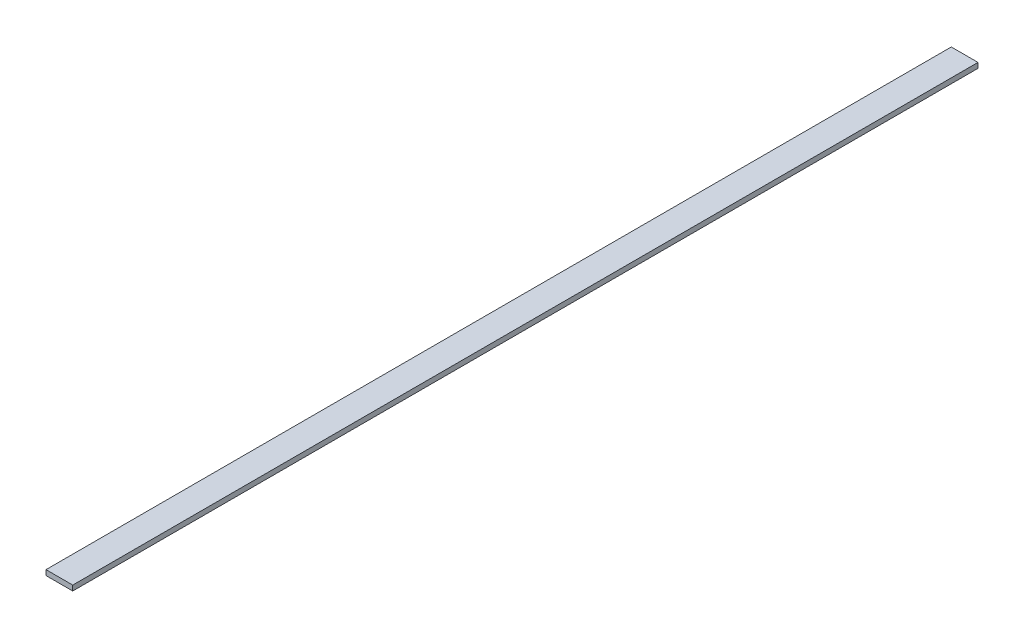
SolidWorks part; units mm, degrees
material "ABS"
ref_plane "Alzado" through (0, 0, 0) normal (0, 0, 1) x (1, 0, 0)
ref_plane "Planta" through (0, 0, 0) normal (0, 1, 0) x (1, 0, 0)
ref_plane "Vista lateral" through (0, 0, 0) normal (1, 0, 0) x (0, 0, -1)
sketch "Croquis1" plane through (0, 0, 0) normal (0, 0, 1) x (1, 0, 0)
  line L1 (0, 0) -> (31, 0)
  line L2 (0, 0) -> (0, 6)
  line L3 (0, 6) -> (31, 6)
  line L4 (31, 0) -> (31, 6)
  dimension "D1" = 31
  dimension "D2" = 6
extrude "Saliente-Extruir1" add sketch "Croquis1" against normal blind 1050
